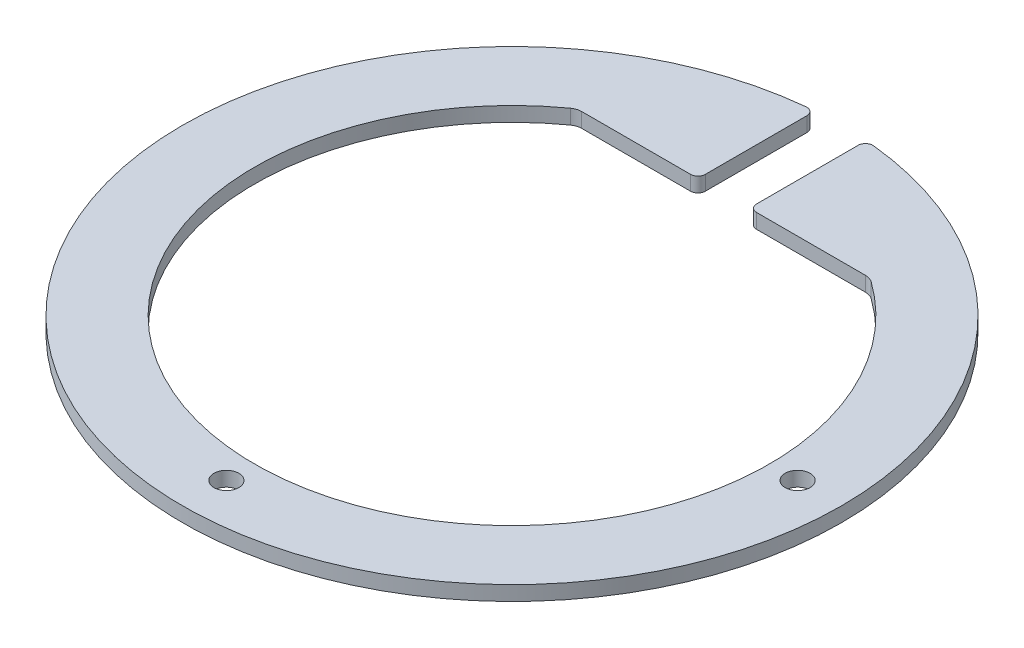
SolidWorks part; units mm, degrees
ref_plane "Plan de face" through (0, 0, 0) normal (0, 0, 1) x (1, 0, 0)
ref_plane "Plan de dessus" through (0, 0, 0) normal (0, 1, 0) x (1, 0, 0)
ref_plane "Plan de droite" through (0, 0, 0) normal (1, 0, 0) x (0, 0, -1)
sketch "Esquisse1" plane through (0, 0, 0) normal (0, 1, 0) x (1, 0, 0)
  line L0 (0, 0) -> (0, 45) construction
  line L1 (20, 28.89) -> (-20, 28.89) construction
  line L2 (-3.5, 28.89) -> (3.5, 28.89) construction
  line L3 (-3.5, 28.89) -> (-3.5, 44.8637)
  line L4 (-3.5, 44.8637) -> (3.5, 44.8637) construction
  line L5 (3.5, 28.89) -> (3.5, 44.8637)
  line L6 (-3.5, 28.89) -> (3.5, 44.8637) construction
  line L7 (-3.5, 44.8637) -> (3.5, 28.89) construction
  line L8 (-20, 28.89) -> (-3.5, 28.89)
  line L9 (3.5, 28.89) -> (20, 28.89)
  circle A0 centre (0, 0) radius 45 construction
  circle A1 centre (0, 0) radius 35.1373 construction
  arc A2 (-20, 28.89) -> (20, 28.89) centre (0, 0) ccw
  arc A3 (-3.5, 44.8637) -> (3.5, 44.8637) centre (0, 0) ccw
  point P3 (0, 36.8768)
  point P12 (0, 28.89)
  dimension "D1" = 90
  dimension "D2" = 28.89
  dimension "D3" = 7
  dimension "D4" = 40
extrude "Boss.-Extru.1" add sketch "Esquisse1" along normal blind 2
sketch "Esquisse2" plane through (0, 2, 0) normal (0, 1, 0) x (1, 0, 0)
  line L0 (0, 0) -> (0, -39) construction
  line L1 (0, 0) -> (39, 0) construction
  line L2 (39, 0) -> (45, 0) construction
  circle A0 centre (39, 0) radius 1.7
  circle A1 centre (0, -39) radius 1.7
  arc A2 (-3.5, 44.8637) -> (3.5, 44.8637) centre (0, 0) ccw construction
  point P9 (45, 0)
  point P10 (0, -45)
  dimension "D1" = 3.4
  dimension "D2" = 3.4
  dimension "D3" = 6
  dimension "D4" = 6
extrude "Enlèv. mat.-Extru.1" cut sketch "Esquisse2" against normal through all
fillet "Congé1" radius 1 4 edges at (3.5, 1, -44.8637) (-3.5, 1, -44.8637) (3.5, 1, -28.89) (-3.5, 1, -28.89)
fillet "Congé2" radius 2 2 edges at (20, 1, -28.89) (-20, 1, -28.89)
